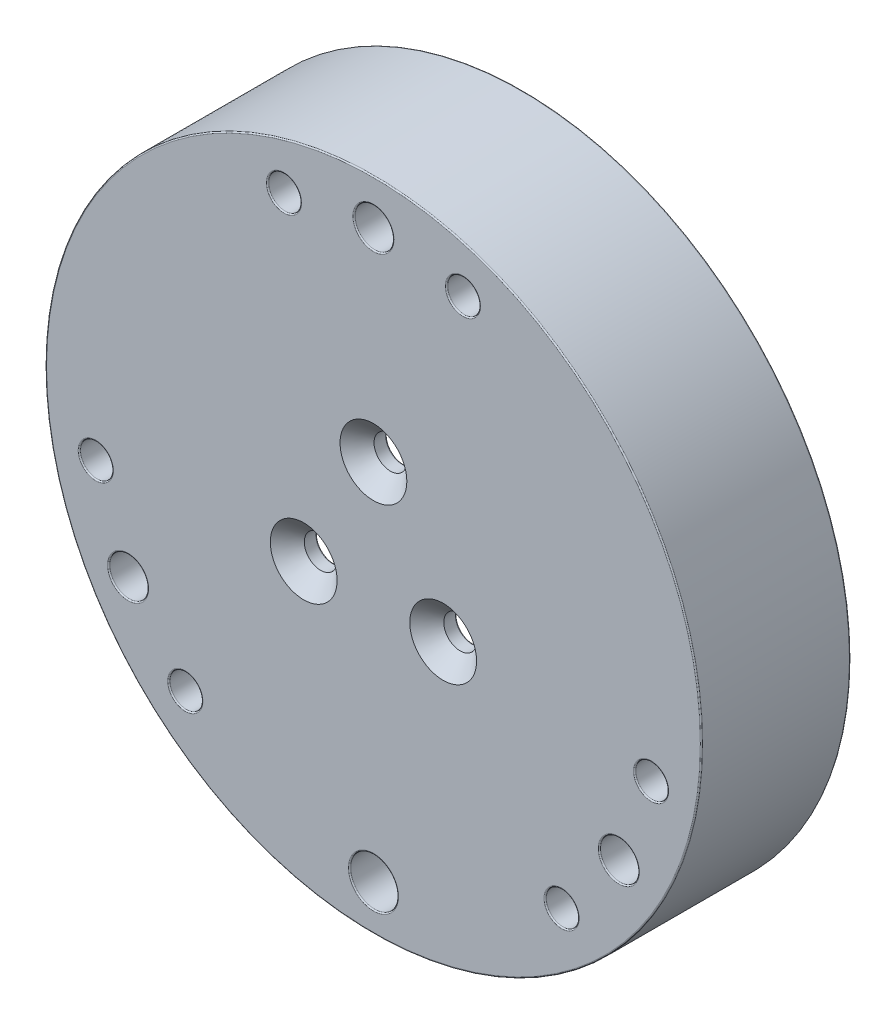
SolidWorks part; units mm, degrees
ref_plane "Alzado" through (0, 0, 0) normal (0, 0, 1) x (1, 0, 0)
ref_plane "Planta" through (0, 0, 0) normal (0, 1, 0) x (1, 0, 0)
ref_plane "Vista lateral" through (0, 0, 0) normal (1, 0, 0) x (0, 0, -1)
sketch "Croquis1" plane through (0, 0, 0) normal (0, 0, 1) x (1, 0, 0)
  circle A0 centre (0, 0) radius 55
  circle A1 centre (0, 0) radius 52.5
  dimension "D1" = 110
  dimension "D2" = 105
extrude "Saliente-Extruir1" add sketch "Croquis1" along normal blind 20
sketch "Croquis2" plane through (0, 0, 20) normal (0, 0, 1) x (1, 0, 0)
  circle A0 centre (0, 0) radius 55
  dimension "D1" = 110
extrude "Saliente-Extruir2" add sketch "Croquis2" along normal blind 5
sketch "Croquis3" plane through (0, 0, 25) normal (0, 0, 1) x (1, 0, 0)
  circle A0 centre (0, 0) radius 13.5
  point P3 (0, 13.5)
  point P4 (11.6913, -6.75)
  point P7 (-11.6913, -6.75)
  point P8 (0, 0)
  dimension "D1" = 27
  dimension "D2" = 3
sketch "Croquis10" plane through (0, 0, 20) normal (0, 0, -1) x (-1, 0, 0)
  line L0 (0, 45) -> (0, 51) construction
  line L1 (-3.5, 45) -> (-3.5, 51)
  line L2 (3.5, 45) -> (3.5, 51)
  line L3 (38.9711, -22.5) -> (44.1673, -25.5) construction
  line L4 (40.7211, -19.4689) -> (45.9173, -22.4689)
  line L5 (37.2211, -25.5311) -> (42.4173, -28.5311)
  line L6 (-38.9711, -22.5) -> (-44.1673, -25.5) construction
  line L7 (-37.2211, -25.5311) -> (-42.4173, -28.5311)
  line L8 (-40.7211, -19.4689) -> (-45.9173, -22.4689)
  line L10 (0, -50.0307) -> (0, -38.3709) construction
  line L11 (-4.5, -50.0307) -> (-4.5, -38.3709)
  line L12 (4.5, -50.0307) -> (4.5, -38.3709)
  arc A1 (-3.5, 45) -> (3.5, 45) centre (0, 45) ccw
  arc A2 (-4.5, -50.0307) -> (4.5, -50.0307) centre (0, -50.0307) ccw
  arc A3 (3.5, 51) -> (-3.5, 51) centre (0, 51) ccw
  arc A4 (40.7211, -19.4689) -> (37.2211, -25.5311) centre (38.9711, -22.5) ccw
  arc A5 (42.4173, -28.5311) -> (45.9173, -22.4689) centre (44.1673, -25.5) ccw
  arc A6 (-37.2211, -25.5311) -> (-40.7211, -19.4689) centre (-38.9711, -22.5) ccw
  arc A7 (-45.9173, -22.4689) -> (-42.4173, -28.5311) centre (-44.1673, -25.5) ccw
  arc A8 (4.5, -38.3709) -> (-4.5, -38.3709) centre (0, -38.3709) ccw
  point P6 (0, 48)
  point P15 (0, -44.2008)
  point P17 (41.5692, -24)
  point P24 (-41.5692, -24)
  point P29 (0, 0)
  circle M7 centre (0, 0) radius 52.5
  dimension "D1" = 3.5
  dimension "D4" = 4.5
  dimension "D2" = 6
  dimension "D3" = 3
hole_wizard "Refrentado para tornillo tapón con cabeza plana de clavija de M51" positions "Croquis7" profile "Croquis6" countersink size "M5" standard "Ansi Metric" end condition through all
sketch "Croquis7" plane through (0, 0, 25) normal (0, 0, 1) x (1, 0, 0)
  point P0 (0, 13.5)
  point P3 (-11.6913, -6.75)
  point P6 (11.6913, -6.75)
sketch "Croquis6" plane through (0, 13.5, 25) normal (1, 0, 0) x (0, -1, 0)
  line L0 (0, 0) -> (0, 25)
  line L1 (0, 25) -> (2.75, 25)
  line L2 (2.75, 25) -> (2.75, 2.85)
  line L3 (2.75, 2.85) -> (5.6, 0)
  line L5 (5.6, 0) -> (0, 0)
  line L6 (-2.75, 2.85) -> (-5.6, 0) construction
  line L11 (0, -6.35) -> (0, 107.95) construction
  dimension "Diámetro de taladro hasta el siguiente" = 5.5
  dimension "Profundidad de taladro hasta el siguiente" = 25
  dimension "Diámetro de avellanado cercano" = 11.2
  dimension "Ángulo de avellanado cercano" = 90
extrude "Saliente-Extruir8" add sketch "Croquis10" along normal blind 10 contours L12 A8 L11 A2 M7 | L5 A5 L4 A4 | L7 A7 L8 A6 | L1 A3 L2 A1
sketch "Croquis12" plane through (0, 0, 25) normal (0, 0, 1) x (1, 0, 0)
  line L0 (0, 47.5) -> (0, 52.082) construction
  line L1 (-11.8522, 45.4873) -> (-13.788, 48.0044)
  line L2 (-13.788, 48.0044) -> (-16.9358, 47.5865)
  line L3 (-16.9358, 47.5865) -> (-18.1478, 44.6515)
  line L4 (-18.1478, 44.6515) -> (-16.212, 42.1344)
  line L5 (-16.212, 42.1344) -> (-13.0642, 42.5522)
  line L6 (-13.0642, 42.5522) -> (-11.8522, 45.4873)
  line L7 (18.1478, 44.6515) -> (16.212, 42.1344)
  line L8 (16.9358, 47.5865) -> (18.1478, 44.6515)
  line L9 (13.788, 48.0044) -> (16.9358, 47.5865)
  line L10 (11.8522, 45.4873) -> (13.788, 48.0044)
  line L11 (13.0642, 42.5522) -> (11.8522, 45.4873)
  line L12 (16.212, 42.1344) -> (13.0642, 42.5522)
  circle A0 centre (0, 0) radius 47.5
  circle A1 centre (0, 47.5) radius 3.25
  circle A2 centre (41.1362, -23.75) radius 3.25
  circle A3 centre (-41.1362, -23.75) radius 3.25
  circle A4 centre (0, -47.5) radius 4
  circle A5 centre (-15, 45.0694) radius 2.75 construction
  circle A6 centre (15, 45.0694) radius 2.75 construction
  point P12 (0, 0)
  dimension "D1" = 95
  dimension "D2" = 6.5
  dimension "D4" = 8
  dimension "D5" = 5.5
  dimension "D6" = 15
  dimension "D3" = 3
extrude "Cortar-Extruir4" cut sketch "Croquis12" against normal blind 10 contours A3 | A2 | A1 | A4
sketch "Croquis16" plane through (0, 0, 25) normal (0, 0, 1) x (1, 0, 0)
  line L0 (0, 44.25) -> (0, 53.0661) construction
  circle A0 centre (-15.0036, 45.0889) radius 2.75
  circle A1 centre (0, 47.5) radius 3.25 construction
  circle A2 centre (15.0036, 45.0889) radius 2.75
  circle A3 centre (46.5499, -9.551) radius 2.75
  circle A4 centre (31.5464, -35.5379) radius 2.75
  circle A5 centre (-31.5464, -35.5379) radius 2.75
  circle A6 centre (-46.5499, -9.551) radius 2.75
  point P21 (0, 0)
  dimension "D1" = 5.5
  dimension "D2" = 3
extrude "Cortar-Extruir7" cut sketch "Croquis16" against normal blind 5
fillet "Redondeo1" radius 0.2 69 edges at (-46.5005, -22.8911, 20) (-43.3192, -20.9689, 20) (-43.0745, -28.825, 20) (-39.8192, -27.0311, 20) (-46.5005, -22.8911, 10) (-43.3192, -20.9689, 10) (-43.0745, -28.825, 10) (-39.8192, -27.0311, 10) (3.426, 51.7161, 20) (3.5, 48, 20) (-3.426, 51.7161, 20) (-3.5, 48, 20) (3.426, 51.7161, 10) (3.5, 48, 10) (-3.426, 51.7161, 10) (-3.5, 48, 10) (46.5005, -22.8911, 10) (43.3192, -20.9689, 10) (35.9401, -20.75, 10) (43.0745, -28.825, 10) (46.5005, -22.8911, 20) (43.3192, -20.9689, 20) (35.9401, -20.75, 20) (43.0745, -28.825, 20) (4.3347, -51.239, 20) (-4.3347, -51.239, 20) (-4.5, -44.2008, 20) (0, -33.8709, 20) (4.3347, -51.239, 10) (4.5, -44.2008, 10) (0, -33.8709, 10) (-4.5, -44.2008, 10) (-37.8862, -23.75, 25) (12.2536, 45.0889, 25) (12.2536, 45.0889, 20) (3.25, 47.5, 25) (3.25, 47.5, 15) (-12.2536, 45.0889, 25) (-12.2536, 45.0889, 20) (49.2999, -9.551, 25) (49.2999, -9.551, 20) (44.3862, -23.75, 25) (44.3862, -23.75, 15) (28.7964, -35.5379, 25) (28.7964, -35.5379, 20) (4, -47.5, 25) (4, -47.5, 15) (-49.2999, -9.551, 25) (-49.2999, -9.551, 20) (55, 0, 0) (52.5, 0, 0) (-45.4663, 26.25, 20) (45.4663, 26.25, 20) (26.5291, -45.3041, 20) (-26.5291, -45.3041, 20) (55, 0, 25) (14.4413, -6.75, 20) (2.75, 13.5, 20) (-8.9413, -6.75, 20) (-35.9401, -20.75, 20) (-35.9401, -20.75, 10) (0, 41.5, 20) (0, 41.5, 10) (39.8192, -27.0311, 10) (39.8192, -27.0311, 20) (4.5, -44.2008, 20) (-4.3347, -51.239, 10) (-28.7964, -35.5379, 20) (-28.7964, -35.5379, 25)
